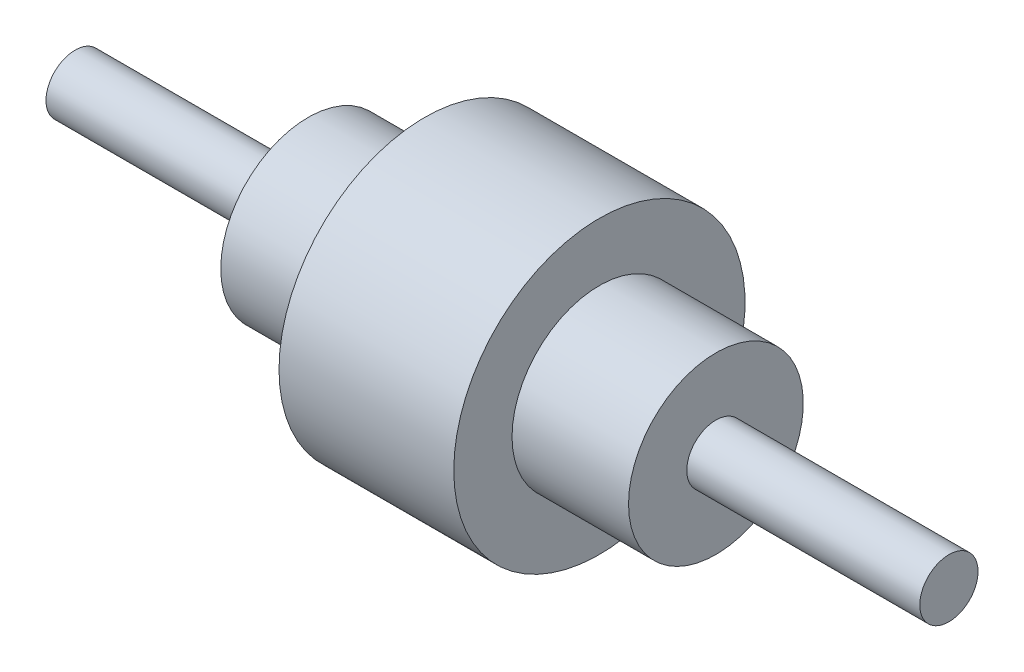
SolidWorks part; units mm, degrees
ref_plane "Front Plane" through (0, 0, 0) normal (0, 0, 1) x (1, 0, 0)
ref_plane "Top Plane" through (0, 0, 0) normal (0, 1, 0) x (1, 0, 0)
ref_plane "Right Plane" through (0, 0, 0) normal (1, 0, 0) x (0, 0, -1)
sketch "Sketch1" plane through (0, 0, 0) normal (0, 0, 1) x (1, 0, 0)
  line L0 (0, 0) -> (332.6334, 0) construction
  line L1 (300, 0) -> (300, -10)
  line L2 (300, -10) -> (220, -10)
  line L3 (220, -10) -> (220, -30)
  line L4 (220, -30) -> (180, -30)
  line L5 (180, -30) -> (180, -50)
  line L6 (180, -50) -> (120, -50)
  line L7 (120, -50) -> (120, -30)
  line L8 (120, -30) -> (80, -30)
  line L9 (80, -30) -> (80, -10)
  line L10 (80, -10) -> (0, -10)
  line L11 (0, -10) -> (0, 0)
  line L12 (300, 0) -> (0, 0)
  dimension "D1" = 300
  dimension "D2" = 80
  dimension "D3" = 40
  dimension "D4" = 60
  dimension "D5" = 40
  dimension "D6" = 80
  dimension "D7" = 20
  dimension "D8" = 60
  dimension "D9" = 100
revolve "Revolve1" add sketch "Sketch1" angle 360 about L0
